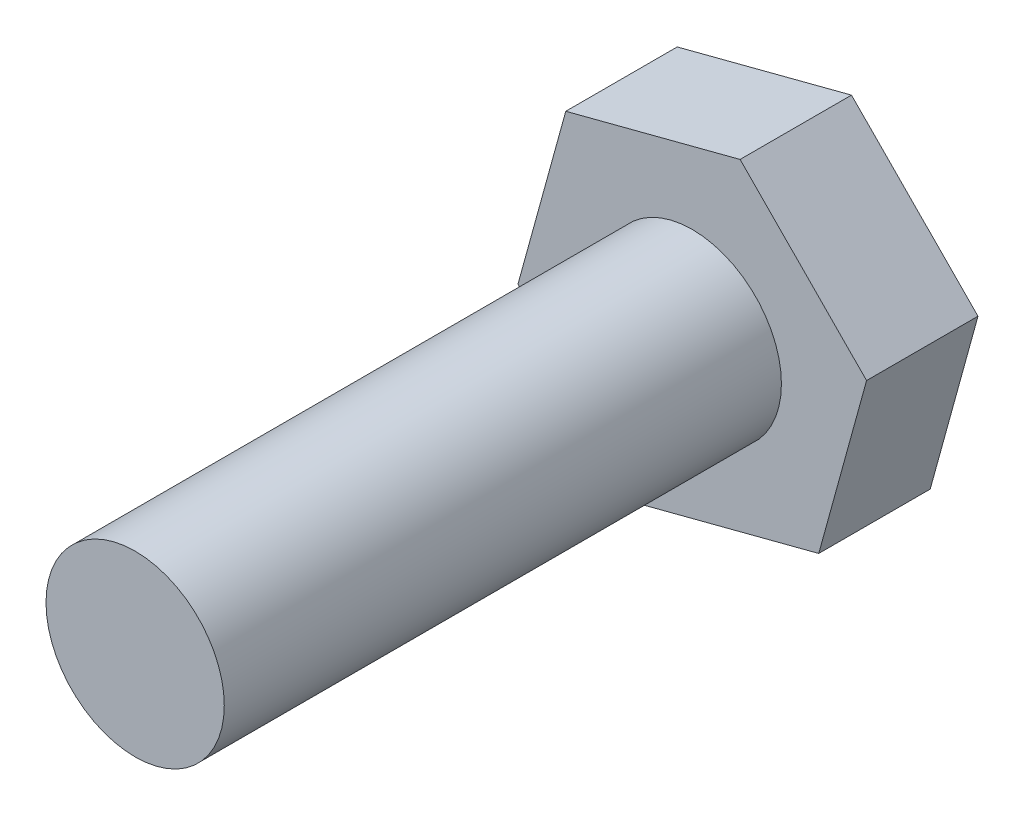
SolidWorks part; units mm, degrees
ref_plane "Front Plane" through (0, 0, 0) normal (0, 0, 1) x (1, 0, 0)
ref_plane "Top Plane" through (0, 0, 0) normal (0, 1, 0) x (1, 0, 0)
ref_plane "Right Plane" through (0, 0, 0) normal (1, 0, 0) x (0, 0, -1)
sketch "Sketch1" plane through (0, 0, 0) normal (0, 0, 1) x (1, 0, 0)
  line L1 (5.6762, -5.7545) -> (7.8216, 2.0385)
  line L2 (7.8216, 2.0385) -> (2.1454, 7.793)
  line L3 (2.1454, 7.793) -> (-5.6762, 5.7545)
  line L4 (-5.6762, 5.7545) -> (-7.8216, -2.0385)
  line L5 (-7.8216, -2.0385) -> (-2.1454, -7.793)
  line L6 (-2.1454, -7.793) -> (5.6762, -5.7545)
  circle A0 centre (0, 0) radius 7 construction
  dimension "D1" = 14
extrude "Boss-Extrude1" add sketch "Sketch1" along normal blind 5
sketch "Sketch2" plane through (0, 0, 5) normal (0, 0, 1) x (1, 0, 0)
  circle A0 centre (0, 0) radius 4
  dimension "D1" = 8
extrude "Boss-Extrude2" add sketch "Sketch2" along normal blind 25
